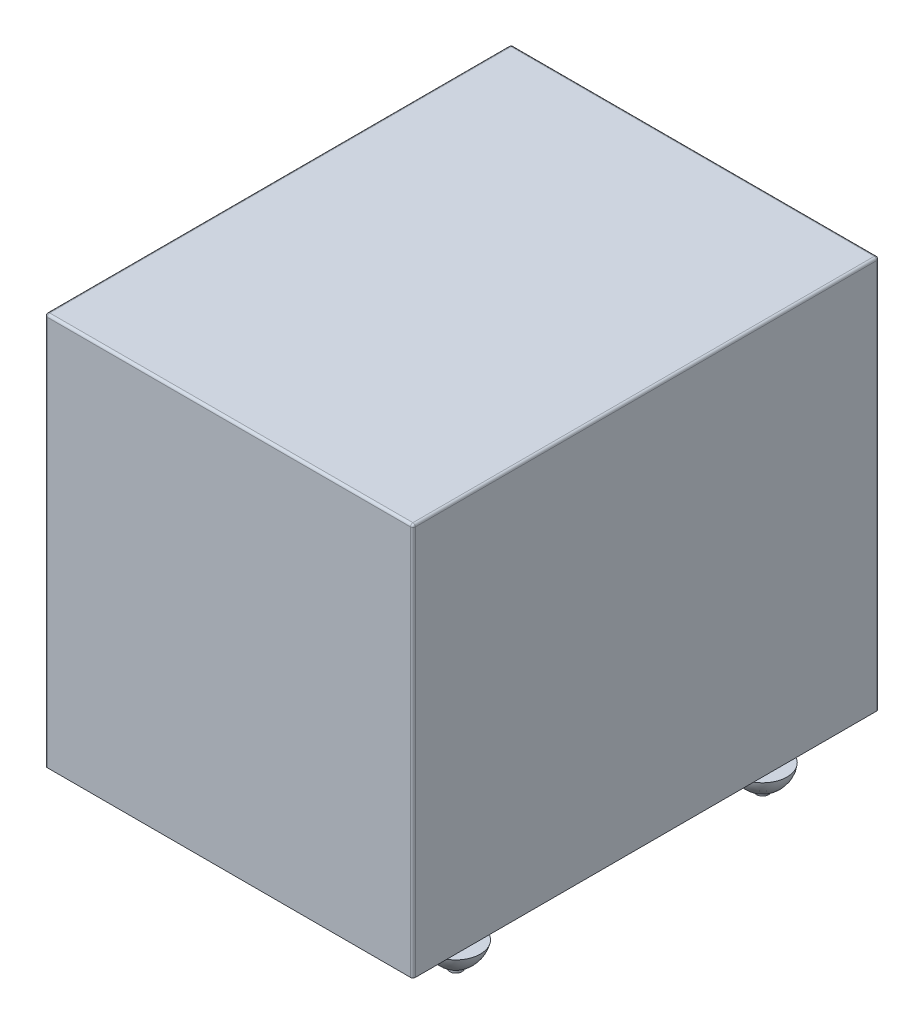
SolidWorks part; units mm, degrees
ref_plane "Ön Düzlem" through (0, 0, 0) normal (0, 0, 1) x (1, 0, 0)
ref_plane "Üst Düzlem" through (0, 0, 0) normal (0, 1, 0) x (1, 0, 0)
ref_plane "Sağ Düzlem" through (0, 0, 0) normal (1, 0, 0) x (0, 0, -1)
sketch "Çizim1" plane through (0, 0, 0) normal (0, 1, 0) x (1, 0, 0)
  line L1 (-7.5, 9.5) -> (7.5, 9.5)
  line L2 (-7.5, 9.5) -> (-7.5, -9.5)
  line L3 (-7.5, -9.5) -> (7.5, -9.5)
  line L4 (7.5, 9.5) -> (7.5, -9.5)
  line L5 (-7.5, 9.5) -> (7.5, -9.5) construction
  line L6 (-7.5, -9.5) -> (7.5, 9.5) construction
  point P0 (0, 0)
  dimension "D1" = 15
  dimension "D2" = 19
extrude "Yükseklik-Ekstrüzyon1" add sketch "Çizim1" along normal blind 16
fillet "Radyus1" radius 0.1 8 edges at (-7.5, 8, -9.5) (-7.5, 8, 9.5) (7.5, 8, -9.5) (7.5, 8, 9.5) (-7.5, 16, 0) (0, 16, -9.5) (7.5, 16, 0) (0, 16, 9.5)
sketch "Çizim2" plane through (0, 0, 0) normal (0, -1, 0) x (1, 0, 0)
  line L0 (0, 0) -> (0, 9.5) construction
  line L1 (-7.4, 9.5) -> (7.4, 9.5) construction
  line L2 (0, 9.5) -> (0, 0) construction
  line L3 (0, 0) -> (7.5, 0) construction
  line L4 (7.5, 9.4) -> (7.5, -9.4) construction
  line L5 (0, 6.25) -> (7.5, 6.25) construction
  line L6 (6, 9.5) -> (6, 0) construction
  line L7 (-6, -6.25) -> (6, -6.25) construction
  line L8 (0, -6.25) -> (0, -8.25) construction
  circle A0 centre (6, 6.25) radius 0.25
  circle A1 centre (-6, 6.25) radius 0.25
  circle A2 centre (6, -6.25) radius 0.25
  circle A3 centre (-6, -6.25) radius 0.25
  circle A4 centre (0, -8.25) radius 0.25
  dimension "D3" = 0.5
  dimension "D5" = 0.5
  dimension "D1" = 6
  dimension "D2" = 6.25
  dimension "D4" = 2
extrude "Yükseklik-Ekstrüzyon2" add sketch "Çizim2" along normal blind 2
ref_plane "Düzlem1" through (-6, 0, 0) normal (-1, 0, 0) x (0, 0, 1)
sketch "Çizim3" plane through (-6, 0, 0) normal (-1, 0, 0) x (0, 0, 1)
  line L0 (-6.25, -2) -> (-6.25, -1)
  line L1 (-6.5, -2) -> (-6, -2) construction
  line L2 (-6.25, -1) -> (-5.25, -1)
  line L3 (0, 0) -> (0, 3.5316) construction
  spline S0 degree 2 poles (-6.25, -2) (-5.44, -1.6284) (-5.25, -1) knots 0 0 0 0.619924 0.619924 0.619924
  dimension "D1" = 1
  dimension "D2" = 1
revolve "Döndür1" add sketch "Çizim3" angle 360 about L0
sketch "Çizim4" plane through (-6, 0, 0) normal (-1, 0, 0) x (0, 0, 1)
  line L0 (6.25, -2) -> (6.25, -1)
  line L1 (6, -2) -> (6.5, -2) construction
  line L2 (6.25, -1) -> (7.25, -1)
  spline S0 degree 2 poles (6.25, -2) (7.0648, -1.6304) (7.25, -1) knots 0 0 0 0.629618 0.629618 0.629618
  dimension "D1" = 1
  dimension "D2" = 1
revolve "Döndür2" add sketch "Çizim4" angle 360 about L0
ref_plane "Düzlem2" through (6, 0, 0) normal (1, 0, 0) x (0, 0, -1)
sketch "Çizim5" plane through (6, 0, 0) normal (1, 0, 0) x (0, 0, -1)
  line L0 (-6.25, -2) -> (-6.25, -1)
  line L1 (-6.5, -2) -> (-6, -2) construction
  line L2 (-6.25, -1) -> (-7.25, -1)
  spline S0 degree 2 poles (-6.25, -2) (-7.1083, -1.6484) (-7.25, -1) knots 0 0 0 0.716604 0.716604 0.716604
  dimension "D1" = 1
  dimension "D2" = 1
revolve "Döndür3" add sketch "Çizim5" angle 360 about L0
sketch "Çizim6" plane through (6, 0, 0) normal (1, 0, 0) x (0, 0, -1)
  line L0 (6.25, -2) -> (6.25, -1)
  line L1 (6, -2) -> (6.5, -2) construction
  line L2 (7.25, -1) -> (5.25, -1) construction
  line L3 (6.25, -1) -> (7.25, -1)
  spline S0 degree 2 poles (6.25, -2) (7.1692, -1.6736) (7.25, -1) knots 0 0 0 0.838321 0.838321 0.838321
revolve "Döndür4" add sketch "Çizim6" angle 360 about L0
ref_plane "Düzlem3" through (0, 0, 0) normal (1, 0, 0) x (0, 0, -1)
sketch "Çizim7" plane through (0, 0, 0) normal (1, 0, 0) x (0, 0, -1)
  line L0 (8.25, -2) -> (8.25, -1)
  line L1 (8, -2) -> (8.5, -2) construction
  line L2 (8.25, -1) -> (9.25, -1)
  spline S0 degree 2 poles (9.25, -1) (8.8542, -1.6512) (8.25, -2) knots 0 0 0 0.71623 0.71623 0.71623
  dimension "D1" = 1
  dimension "D2" = 1
revolve "Döndür5" add sketch "Çizim7" angle 360 about L0
